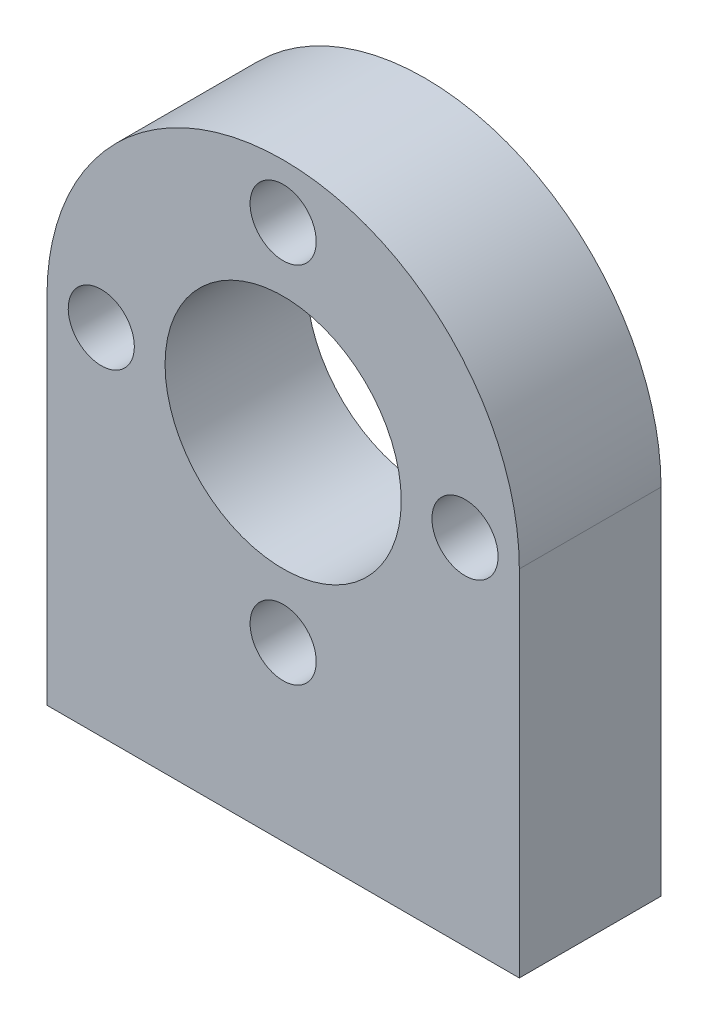
SolidWorks part; units mm, degrees
material "PET"
ref_plane "Front Plane" through (0, 0, 0) normal (0, 0, 1) x (1, 0, 0)
ref_plane "Top Plane" through (0, 0, 0) normal (0, 1, 0) x (1, 0, 0)
ref_plane "Right Plane" through (0, 0, 0) normal (1, 0, 0) x (0, 0, -1)
sketch "Sketch1" plane through (0, 0, 0) normal (0, 0, 1) x (1, 0, 0)
  line L1 (0, 0) -> (-25.4, 0)
  line L2 (0, 0) -> (0, -31.75)
  line L3 (0, -31.75) -> (-25.4, -31.75)
  line L4 (-25.4, 0) -> (-25.4, -31.75)
  circle A0 centre (-12.7, -12.7) radius 12.7
  dimension "D3" = 19.05
  dimension "D5" = 25.4
  dimension "D1" = 31.75
  dimension "D2" = 25.4
  dimension "D4" = 12.7
extrude "Boss-Extrude1" add sketch "Sketch1" along normal blind 7.62 contours A0 L4 L3 L2 | A0
sketch "Sketch2" plane through (0, 0, 7.62) normal (0, 0, 1) x (1, 0, 0)
  line L0 (0, -31.75) -> (-25.4, -31.75) construction
  line L1 (-25.4, -12.7) -> (-25.4, -31.75) construction
  circle A0 centre (-12.7, -12.7) radius 6.35
  dimension "D1" = 12.7
  dimension "D2" = 19.05
  dimension "D3" = 12.7
extrude "Cut-Extrude1" cut sketch "Sketch2" against normal blind 7.62
sketch "Sketch3" plane through (0, 0, 7.62) normal (0, 0, 1) x (1, 0, 0)
  line L0 (-25.4, -12.7) -> (-25.4, -31.75) construction
  circle A0 centre (-12.7, -2.921) radius 1.778
  circle A1 centre (-12.7, -12.7) radius 6.35 construction
  dimension "D1" = 3.556
  dimension "D2" = 12.7
  dimension "D3" = 9.779
extrude "Cut-Extrude2" cut sketch "Sketch3" against normal blind 7.62
pattern_circular "CirPattern1" count 4 over 360 about axis through (-12.7, -12.7, 0) along (0, 0, 1) of "Cut-Extrude2"
